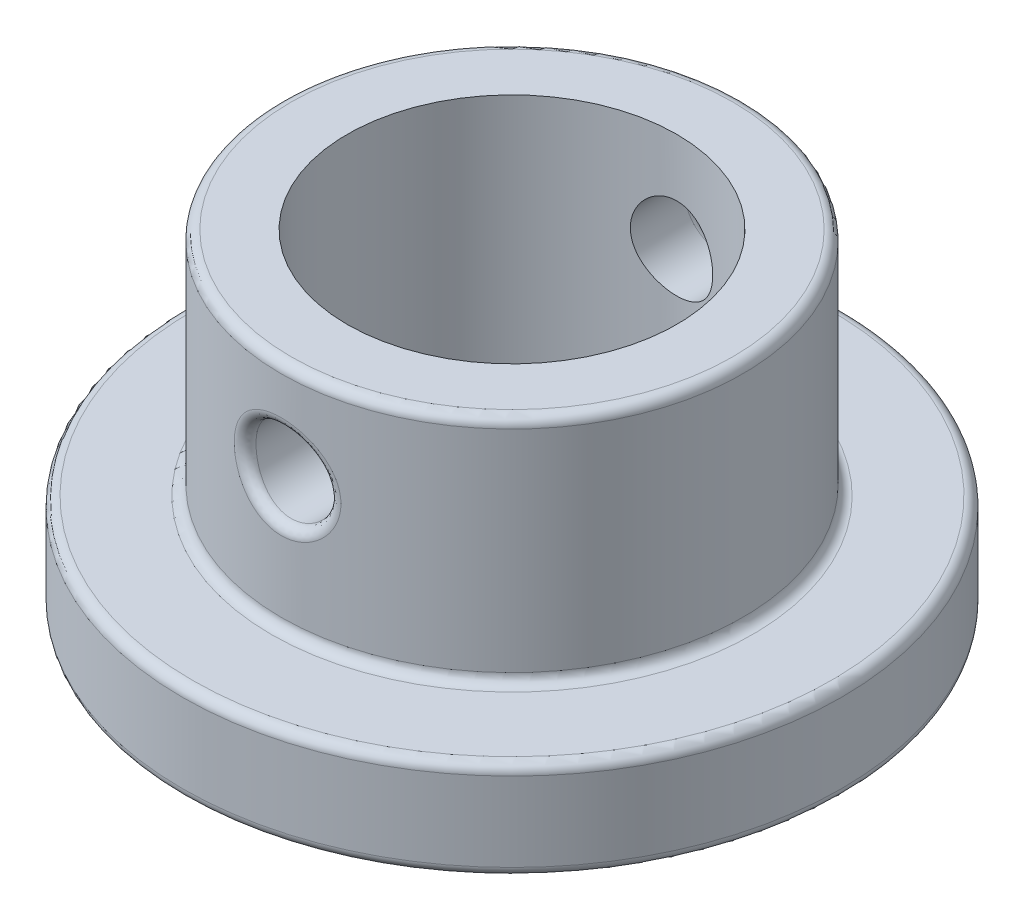
SolidWorks part; units mm, degrees
ref_plane "Front Plane" through (0, 0, 0) normal (0, 0, 1) x (1, 0, 0)
ref_plane "Top Plane" through (0, 0, 0) normal (0, 1, 0) x (1, 0, 0)
ref_plane "Right Plane" through (0, 0, 0) normal (1, 0, 0) x (0, 0, -1)
sketch "Sketch1" plane through (0, 0, 0) normal (0, 1, 0) x (1, 0, 0)
  circle A0 centre (0, 0) radius 5
  circle A1 centre (0, 0) radius 10
  circle A2 centre (0, 0) radius 7 construction
  dimension "D1" = 2
  dimension "D2" = 10
  dimension "D3" = 20
extrude "Boss-Extrude1" add sketch "Sketch1" along normal blind 3
sketch "Sketch2" plane through (0, 3, 0) normal (0, 1, 0) x (1, 0, 0)
  circle A0 centre (0, 0) radius 5
  circle A1 centre (0, 0) radius 7
  dimension "D1" = 10
  dimension "D2" = 2
extrude "Boss-Extrude2" add sketch "Sketch2" along normal blind 7
sketch "Sketch3" plane through (0, 0, 0) normal (0, 0, 1) x (1, 0, 0)
  circle A0 centre (0, 7) radius 1.25
  dimension "D1" = 2.5
  dimension "D2" = 7
extrude "Cut-Extrude1" cut sketch "Sketch3" against normal through all both and the other way through all
fillet "Fillet1" radius 0.3 6 edges at (0, 3, 7) (0, 10, 7) (0.2653, 5.7785, -6.995) (-1.2215, 7.2654, 6.8926) (0, 3, 10) (0, 0, 10)
